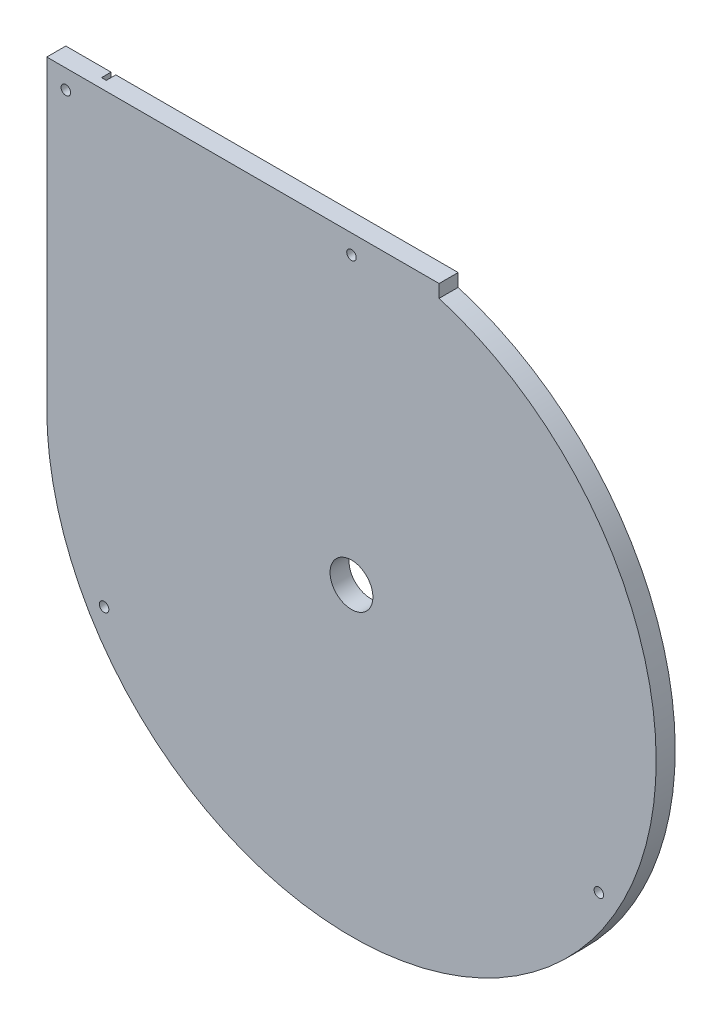
SolidWorks part; units mm, degrees
ref_plane "Front Plane" through (0, 0, 0) normal (0, 0, 1) x (1, 0, 0)
ref_plane "Top Plane" through (0, 0, 0) normal (0, 1, 0) x (1, 0, 0)
ref_plane "Right Plane" through (0, 0, 0) normal (1, 0, 0) x (0, 0, -1)
sketch "Sketch1" plane through (0, 0, 0) normal (0, 0, 1) x (1, 0, 0)
  line L1 (203.2, -203.2) -> (-203.2, -203.2)
  line L2 (203.2, -203.2) -> (203.2, 203.2)
  line L3 (203.2, 203.2) -> (-203.2, 203.2)
  line L4 (-203.2, -203.2) -> (-203.2, 203.2)
  line L5 (203.2, -203.2) -> (-203.2, 203.2) construction
  line L6 (203.2, 203.2) -> (-203.2, -203.2) construction
  point P0 (0, 0)
  dimension "D1" = 406.4
  dimension "D2" = 406.4
extrude "Boss-Extrude1" add sketch "Sketch1" along normal blind 12.7
sketch "Sketch2" plane through (0, 0, 0) normal (0, 0, -1) x (-1, 0, 0)
  line L4 (17.6969, 168.9381) -> (18.0277, 172.0958)
  line L5 (169.8625, 203.2) -> (169.8625, 0)
  line L6 (173.0375, 203.2) -> (169.8625, 203.2)
  line L7 (173.0375, 0) -> (173.0375, 203.2)
  line L8 (17.6969, 168.9381) -> (18.0277, 172.0958)
  line L9 (169.8625, 203.2) -> (169.8625, 0)
  line L10 (173.0375, 203.2) -> (169.8625, 203.2)
  line L11 (173.0375, 0) -> (173.0375, 203.2)
  arc A2 (18.0277, 172.0958) -> (173.0375, 0) centre (0, 0) ccw
  arc A3 (17.6969, 168.9381) -> (169.8625, 0) centre (0, 0) ccw
  arc A4 (18.0277, 172.0958) -> (173.0375, 0) centre (0, 0) ccw
  arc A5 (17.6969, 168.9381) -> (169.8625, 0) centre (0, 0) ccw
  dimension "D1" = 0
extrude "Cut-Extrude1" cut sketch "Sketch2" against normal blind 6.35
sketch "Sketch3" plane through (0, 0, 0) normal (0, 0, -1) x (-1, 0, 0)
  line L1 (-58.4327, 194.6172) -> (-58.4327, 203.2)
  line L6 (-58.4327, 194.6172) -> (-58.4327, 203.2) construction
  line L9 (203.2, -203.2) -> (203.2, 203.2)
  line L10 (-203.2, -203.2) -> (203.2, -203.2)
  line L11 (-203.2, 203.2) -> (-203.2, -203.2)
  line L12 (203.2, 203.2) -> (-203.2, 203.2)
  line L13 (203.2, -203.2) -> (203.2, 203.2)
  line L14 (-203.2, -203.2) -> (203.2, -203.2)
  line L15 (-203.2, 203.2) -> (-203.2, -203.2)
  line L16 (203.2, 203.2) -> (-203.2, 203.2)
  arc A1 (203.2, 0) -> (-58.4327, 194.6172) centre (0, 0) cw
  circle A2 centre (0, 0) radius 14.2875 construction
  circle A3 centre (0, 0) radius 14.2875
  line M3 (169.8625, 203.2) -> (-203.2, 203.2)
  line M4 (-203.2, 203.2) -> (-203.2, -203.2)
  line M5 (-203.2, -203.2) -> (203.2, -203.2)
  line M6 (203.2, -203.2) -> (203.2, 203.2)
  dimension "D2" = 28.575
  dimension "D1" = 0
extrude "Cut-Extrude2" cut sketch "Sketch3" against normal through all contours A1 L14 M6 | A1 L15 M5 | A1 L1 M4 M3 | A3
sketch "Sketch4" plane through (0, 0, 0) normal (0, 0, -1) x (-1, 0, 0)
  circle A0 centre (-164.9778, -95.25) radius 3.175 construction
  circle A1 centre (0, 190.5) radius 3.175 construction
  circle A2 centre (164.9778, -95.25) radius 3.175 construction
  circle A3 centre (190.5, 190.5) radius 3.175 construction
  circle A4 centre (-164.9778, -95.25) radius 3.175
  circle A5 centre (0, 190.5) radius 3.175
  circle A6 centre (164.9778, -95.25) radius 3.175
  circle A7 centre (190.5, 190.5) radius 3.175
extrude "Cut-Extrude3" cut sketch "Sketch4" against normal through all
